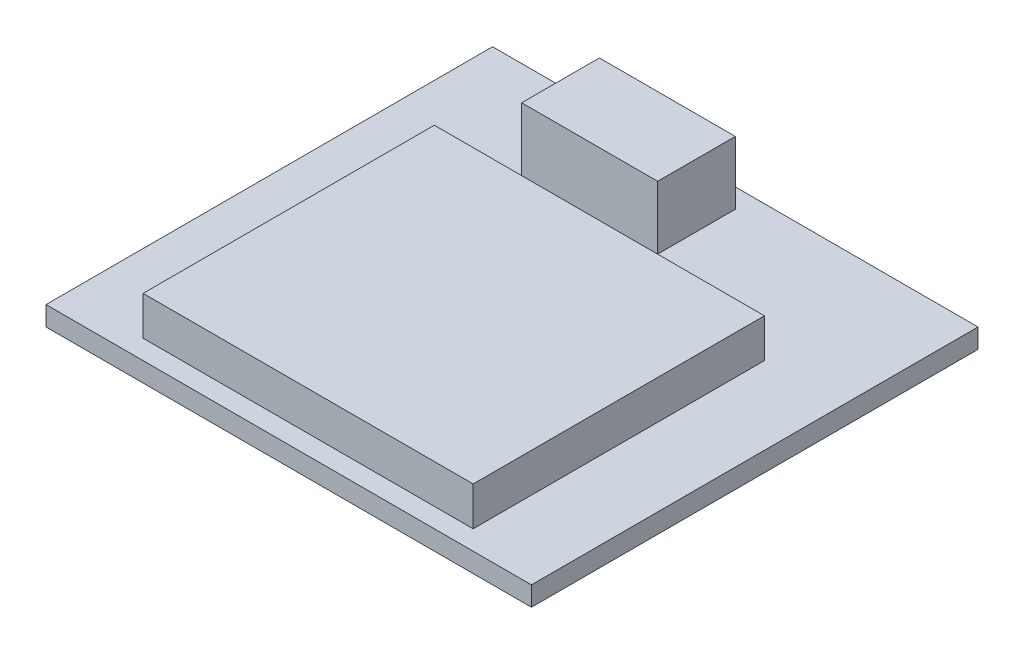
SolidWorks part; units mm, degrees
ref_plane "Front Plane" through (0, 0, 0) normal (0, 0, 1) x (1, 0, 0)
ref_plane "Top Plane" through (0, 0, 0) normal (0, 1, 0) x (1, 0, 0)
ref_plane "Right Plane" through (0, 0, 0) normal (1, 0, 0) x (0, 0, -1)
sketch "Sketch1" plane through (0, 0, 0) normal (0, 1, 0) x (1, 0, 0)
  line L1 (-12.5, -11.5) -> (12.5, -11.5)
  line L2 (-12.5, -11.5) -> (-12.5, 11.5)
  line L3 (-12.5, 11.5) -> (12.5, 11.5)
  line L4 (12.5, -11.5) -> (12.5, 11.5)
  line L5 (-12.5, -11.5) -> (12.5, 11.5) construction
  line L6 (-12.5, 11.5) -> (12.5, -11.5) construction
  point P0 (0, 0)
  dimension "D1" = 25
  dimension "D2" = 23
extrude "Boss-Extrude1" add sketch "Sketch1" along normal blind 1
sketch "Sketch2" plane through (0, 1, 0) normal (0, 1, 0) x (1, 0, 0)
  line L0 (0, -11.5) -> (0, 11.5) construction
  line L1 (-12.5, -11.5) -> (12.5, -11.5) construction
  line L2 (12.5, 11.5) -> (-12.5, 11.5) construction
  line L4 (-8.5, -10.5) -> (8.5, -10.5)
  line L5 (-8.5, -10.5) -> (-8.5, 4.5)
  line L6 (-8.5, 4.5) -> (8.5, 4.5)
  line L7 (8.5, -10.5) -> (8.5, 4.5)
  line L8 (-8.5, -10.5) -> (8.5, 4.5) construction
  line L9 (-8.5, 4.5) -> (8.5, -10.5) construction
  point P6 (0, -3)
  dimension "D1" = 17
  dimension "D2" = 15
  dimension "D3" = 1
extrude "Boss-Extrude2" add sketch "Sketch2" along normal blind 2
sketch "Sketch3" plane through (0, 1, 0) normal (0, 1, 0) x (1, 0, 0)
  line L0 (-12.5, 11.5) -> (-12.5, -11.5) construction
  line L4 (12.5, 11.5) -> (-12.5, 11.5) construction
  line L5 (-6, 10.5) -> (1, 10.5)
  line L6 (-6, 10.5) -> (-6, 6.5)
  line L7 (-6, 6.5) -> (1, 6.5)
  line L8 (1, 10.5) -> (1, 6.5)
  line L9 (-6, 10.5) -> (1, 6.5) construction
  line L10 (-6, 6.5) -> (1, 10.5) construction
  point P8 (-2.5, 8.5)
  dimension "D1" = 7
  dimension "D2" = 4
  dimension "D3" = 6.5
  dimension "D4" = 1
extrude "Boss-Extrude3" add sketch "Sketch3" along normal blind 3.25
sketch "Sketch4" plane through (0, 0, 0) normal (0, -1, 0) x (1, 0, 0)
  line L0 (-12.5, 11.5) -> (12.5, 11.5) construction
  line L1 (0, -11.5) -> (0, 11.5) construction
  line L2 (12.5, -11.5) -> (-12.5, -11.5) construction
  line L4 (7.5, -11.5) -> (-7.5, -11.5)
  line L5 (7.5, -11.5) -> (7.5, 5.5)
  line L6 (7.5, 5.5) -> (-7.5, 5.5)
  line L7 (-7.5, -11.5) -> (-7.5, 5.5)
  line L8 (7.5, -11.5) -> (-7.5, 5.5) construction
  line L9 (7.5, 5.5) -> (-7.5, -11.5) construction
  point P6 (0, -3)
  dimension "D1" = 17
  dimension "D2" = 15
extrude "Boss-Extrude4" add sketch "Sketch4" along normal blind 0.75 separate body
sketch "Sketch5" plane through (0, 0, -11.5) normal (0, 0, -1) x (-1, 0, 0)
  line L0 (7.5, 0) -> (-7.5, 0) construction
  line L2 (-5, -0.1) -> (7.45, -0.1)
  line L5 (-5, -0.1) -> (-5, -0.7)
  line L10 (-5, -0.7) -> (7.45, -0.7)
  line L11 (7.45, -0.1) -> (7.45, -0.7)
  line L12 (-7.5, -0.75) -> (-7.5, 0) construction
  line L14 (7.5, -0.75) -> (7.5, 0) construction
  line L15 (7.5, -0.75) -> (-7.5, -0.75) construction
  dimension "D1" = 0.1
  dimension "D2" = 2.5
  dimension "D3" = 0.05
  dimension "D4" = 0.05
extrude "Cut-Extrude1" cut sketch "Sketch5" against normal blind 16.75
sketch "Sketch6" plane through (0, -0.75, 0) normal (0, -1, 0) x (1, 0, 0)
  circle A0 centre (-5.5474, 3.1436) radius 0.7705
  circle A1 centre (-2.5474, 3.1436) radius 0.7705
  circle A2 centre (0.4526, 3.1436) radius 0.7705
  circle A3 centre (3.4526, 3.1436) radius 0.7705
  circle A4 centre (-2.5474, -6.8564) radius 0.7705
  circle A5 centre (0.4526, -6.8564) radius 0.7705
  circle A6 centre (3.4526, -6.8564) radius 0.7705
  circle A7 centre (-5.5474, -6.8564) radius 0.7705
  dimension "D1" = 4
  dimension "D2" = 2
extrude "Cut-Extrude2" cut sketch "Sketch6" against normal blind 0.5
